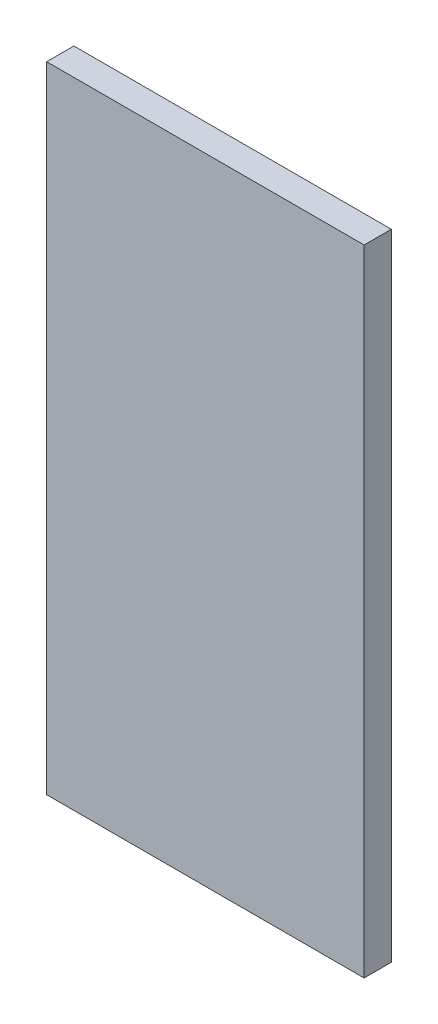
SolidWorks part; units mm, degrees
ref_plane "Plan de face" through (0, 0, 0) normal (0, 0, 1) x (1, 0, 0)
ref_plane "Plan de dessus" through (0, 0, 0) normal (0, 1, 0) x (1, 0, 0)
ref_plane "Plan de droite" through (0, 0, 0) normal (1, 0, 0) x (0, 0, -1)
sketch "Esquisse1" plane through (0, 0, 0) normal (0, 0, 1) x (1, 0, 0)
  line L1 (0, 0) -> (35, 0)
  line L2 (0, 0) -> (0, -70)
  line L3 (0, -70) -> (35, -70)
  line L4 (35, 0) -> (35, -70)
  dimension "D1" = 35
  dimension "D2" = 70
extrude "Boss.-Extru.1" add sketch "Esquisse1" along normal blind 3
